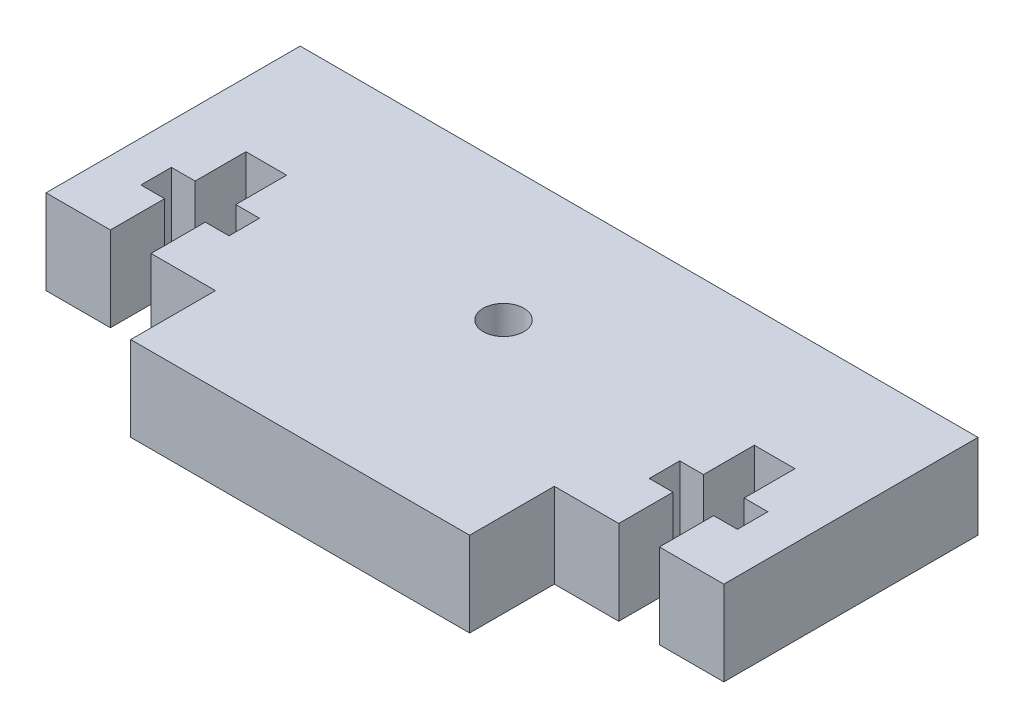
SolidWorks part; units mm, degrees
ref_plane "Front Plane" through (0, 0, 0) normal (0, 0, 1) x (1, 0, 0)
ref_plane "Top Plane" through (0, 0, 0) normal (0, 1, 0) x (1, 0, 0)
ref_plane "Right Plane" through (0, 0, 0) normal (1, 0, 0) x (0, 0, -1)
sketch "Sketch1" plane through (0, 0, 0) normal (0, 1, 0) x (1, 0, 0)
  line L0 (25.4, 0) -> (25.4, -25.4) construction
  line L1 (0, 0) -> (50.8, 0)
  line L2 (0, 0) -> (0, -25.4)
  line L3 (0, -25.4) -> (50.8, -25.4)
  line L4 (50.8, 0) -> (50.8, -25.4)
  line L5 (0, -25.4) -> (12.7, -25.4)
  line L6 (0, -25.4) -> (0, -19.05)
  line L7 (0, -19.05) -> (12.7, -19.05)
  line L8 (12.7, -25.4) -> (12.7, -19.05)
  line L9 (50.8, -25.4) -> (38.1, -25.4)
  line L10 (50.8, -25.4) -> (50.8, -19.05)
  line L11 (50.8, -19.05) -> (38.1, -19.05)
  line L12 (38.1, -25.4) -> (38.1, -19.05)
  line L13 (42.926, -19.05) -> (45.974, -19.05)
  line L14 (42.926, -19.05) -> (42.926, -8.89)
  line L15 (42.926, -8.89) -> (45.974, -8.89)
  line L16 (45.974, -19.05) -> (45.974, -8.89)
  line L17 (41.148, -12.7) -> (47.752, -12.7)
  line L18 (41.148, -12.7) -> (41.148, -14.986)
  line L19 (41.148, -14.986) -> (47.752, -14.986)
  line L20 (47.752, -12.7) -> (47.752, -14.986)
  line L21 (9.652, -14.986) -> (3.048, -14.986)
  line L22 (3.048, -12.7) -> (3.048, -14.986)
  line L23 (9.652, -12.7) -> (3.048, -12.7)
  line L24 (9.652, -12.7) -> (9.652, -14.986)
  line L25 (7.874, -8.89) -> (4.826, -8.89)
  line L26 (4.826, -19.05) -> (4.826, -8.89)
  line L27 (7.874, -19.05) -> (4.826, -19.05)
  line L28 (7.874, -19.05) -> (7.874, -8.89)
  point P15 (44.45, -8.89)
  point P20 (41.148, -13.843)
  point P21 (47.752, -13.843)
  dimension "D1" = 50.8
  dimension "D2" = 25.4
  dimension "D3" = 12.7
  dimension "D4" = 6.35
  dimension "D5" = 12.7
  dimension "D6" = 6.35
  dimension "D7" = 10.16
  dimension "D8" = 6.35
  dimension "D9" = 3.048
  dimension "D10" = 2.286
  dimension "D11" = 4.064
  dimension "D12" = 1.778
  dimension "D13" = 1.778
extrude "Boss-Extrude1" add sketch "Sketch1" along normal blind 6.35 contours L0 L1 L2 L7 L26 L21 L22 L23 L25 L28 L24 L8 L3 | L1 L0 L3 L12 L11 L14 L19 L18 L17 L15 L16 L20 L4
sketch "Sketch2" plane through (0, 6.35, 0) normal (0, 1, 0) x (1, 0, 0)
  line L0 (50.8, 0) -> (50.8, -19.05) construction
  line L1 (0, 0) -> (50.8, 0) construction
  circle A0 centre (25.4, -10.16) radius 1.524
  dimension "D3" = 3.048
  dimension "D1" = 25.4
  dimension "D2" = 10.16
extrude "Cut-Extrude1" cut sketch "Sketch2" against normal through all
